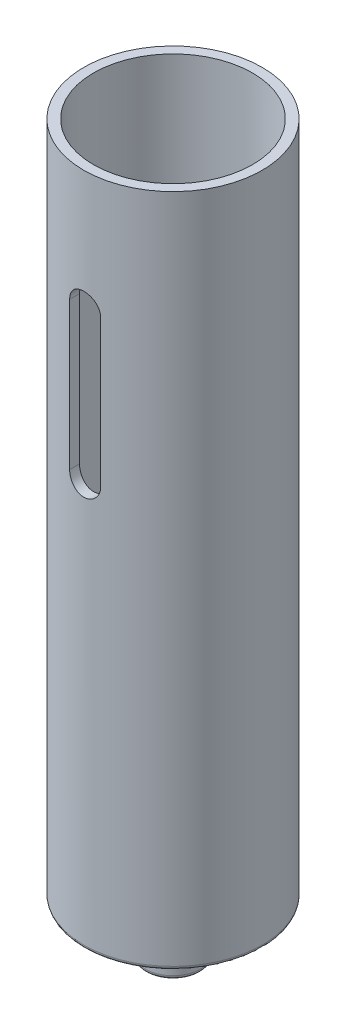
SolidWorks part; units mm, degrees
ref_plane "Front Plane" through (0, 0, 0) normal (0, 0, 1) x (1, 0, 0)
ref_plane "Top Plane" through (0, 0, 0) normal (0, 1, 0) x (1, 0, 0)
ref_plane "Right Plane" through (0, 0, 0) normal (1, 0, 0) x (0, 0, -1)
sketch "Sketch1" plane through (0, 0, 0) normal (0, 1, 0) x (1, 0, 0)
  circle A0 centre (0, 0) radius 11.5
  circle A1 centre (0, 0) radius 10.25
  dimension "D1" = 23
  dimension "D2" = 1.25
extrude "Boss-Extrude1" add sketch "Sketch1" along normal blind 87
sketch "Sketch2" plane through (0, 0, 0) normal (0, -1, 0) x (1, 0, 0)
  circle A0 centre (0, 0) radius 10.25 construction
  circle A1 centre (0, 0) radius 10.25
extrude "Boss-Extrude2" add sketch "Sketch2" against normal blind 1.35
sketch "Sketch3" plane through (0, 0, 0) normal (0, -1, 0) x (1, 0, 0)
  circle A0 centre (0, 0) radius 3.55
  dimension "D1" = 7.1
extrude "Boss-Extrude3" add sketch "Sketch3" along normal blind 6.66
sketch "Sketch4" plane through (0, 0, 0) normal (0, 0, 1) x (1, 0, 0)
  line L0 (11.5, 87) -> (-11.5, 87) construction
  line L2 (-2, 71.5) -> (-2, 52.5)
  line L4 (2, 71.5) -> (2, 52.5)
  line L5 (-2, 71.5) -> (2, 52.5) construction
  line L6 (-2, 52.5) -> (2, 71.5) construction
  line L7 (0, 87) -> (0, 0) construction
  arc A4 (2, 52.5) -> (-2, 52.5) centre (0, 52.5) cw
  arc A5 (-2, 71.5) -> (2, 71.5) centre (0, 71.5) cw
  point P0 (0, 62)
  point P12 (-2.5621, 73.8061)
  point P14 (0, 0)
  point P17 (0, 0)
  point P21 (0, 0)
  point P22 (0, 0)
  point P23 (0.01, 66.5117)
  point P24 (0.01, 64.9318)
  point P25 (0, 0)
  dimension "D3" = 15.5
  dimension "D1" = 4
  dimension "D2" = 19
extrude "Cut-Extrude1" cut sketch "Sketch4" against normal through all both and the other way through all
fillet "Fillet1" radius 0.5 3 edges at (0, -6.66, -3.55) (0, 0, -3.55) (0, 0, 11.5)
